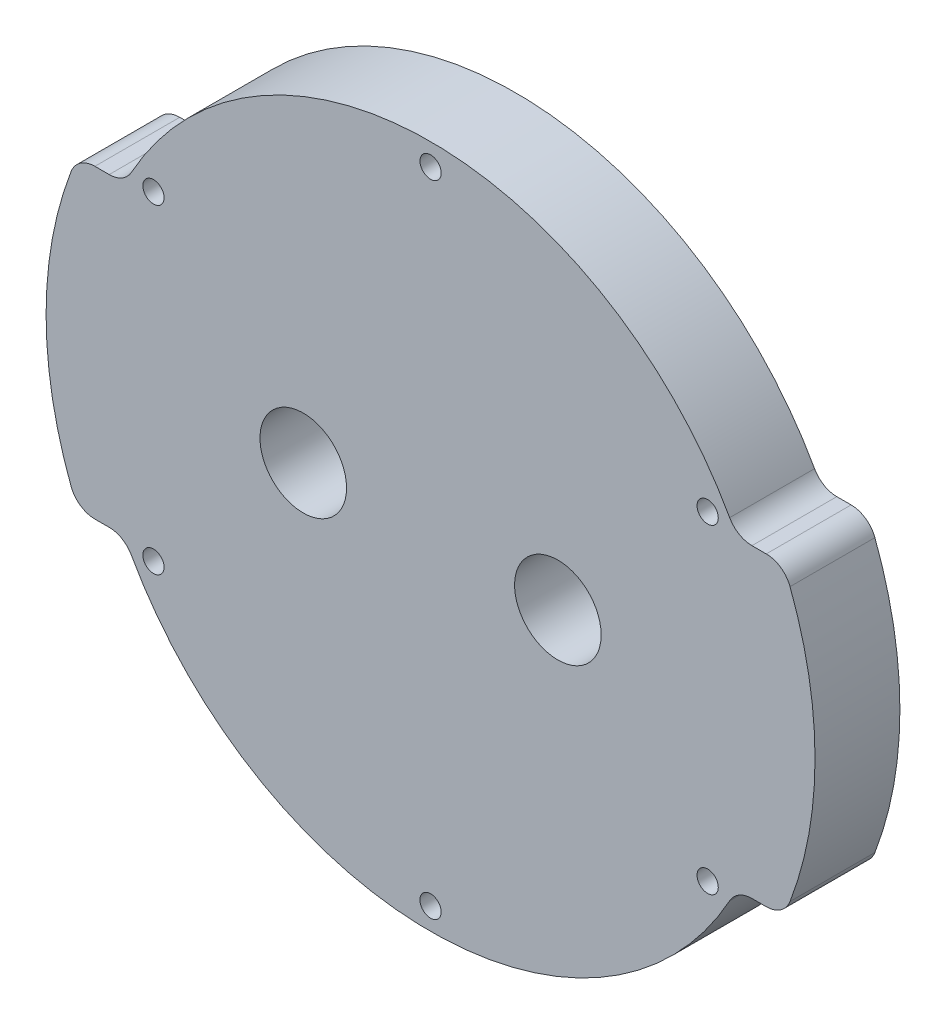
SolidWorks part; units mm, degrees
ref_plane "前视" through (0, 0, 0) normal (0, 0, 1) x (1, 0, 0)
ref_plane "上视" through (0, 0, 0) normal (0, 1, 0) x (1, 0, 0)
ref_plane "右视" through (0, 0, 0) normal (1, 0, 0) x (0, 0, -1)
sketch "草图1" plane through (0, 0, 0) normal (0, 0, 1) x (1, 0, 0)
  circle A0 centre (0, 0) radius 45.3
extrude "凸台-拉伸1" add sketch "草图1" along normal blind 10
sketch "草图2" plane through (0, 0, 10) normal (0, 0, 1) x (1, 0, 0)
  line L0 (-47.3402, 18) -> (55.6392, 18) construction
  line L1 (-63.5717, -18) -> (57.082, -18) construction
  line L2 (-36.0568, 18) -> (-41.5703, 18)
  line L3 (-36.0568, -18) -> (-41.7346, -18)
  line L4 (36.0568, -18) -> (41.7346, -18)
  line L5 (36.0568, 18) -> (41.5703, 18)
  arc A0 (36.0568, 18) -> (-36.0568, 18) centre (0, 0) ccw
  arc A1 (-36.0568, -18) -> (36.0568, -18) centre (0, 0) ccw
  circle A2 centre (0, 0) radius 45.3 construction
  arc A3 (41.5703, 18) -> (-41.5703, 18) centre (0, 0) ccw
  arc A4 (-41.7346, -18) -> (41.7346, -18) centre (0, 0) ccw
  dimension "D1" = 18
  dimension "D2" = 18
extrude "切除-拉伸1" cut sketch "草图2" against normal through all
fillet "圆角1" radius 3 8 edges at (36.0568, 18, 5) (41.5703, 18, 5) (41.5703, -18, 5) (36.0568, -18, 5) (-36.0568, -18, 5) (-41.5703, -18, 5) (-41.5703, 18, 5) (-36.0568, 18, 5)
sketch "草图3" plane through (0, 0, 10) normal (0, 0, 1) x (1, 0, 0)
  circle A0 centre (0, 37.7) radius 1.25
  circle A1 centre (32.6492, 18.85) radius 1.25
  circle A2 centre (32.6492, -18.85) radius 1.25
  circle A3 centre (0, -37.7) radius 1.25
  circle A4 centre (-32.6492, -18.85) radius 1.25
  circle A5 centre (-32.6492, 18.85) radius 1.25
  point P16 (0, 0)
  dimension "D1" = 2.5
  dimension "D2" = 37.7
  dimension "D3" = 6
extrude "切除-拉伸2" cut sketch "草图3" against normal through all
sketch "草图4" plane through (0, 0, 10) normal (0, 0, 1) x (1, 0, 0)
  circle A0 centre (-15, 0) radius 5.1
  circle A1 centre (15, 0) radius 5.1
  point P9 (0, 0)
  dimension "D1" = 15
  dimension "D2" = 2
extrude "切除-拉伸3" cut sketch "草图4" against normal through all
